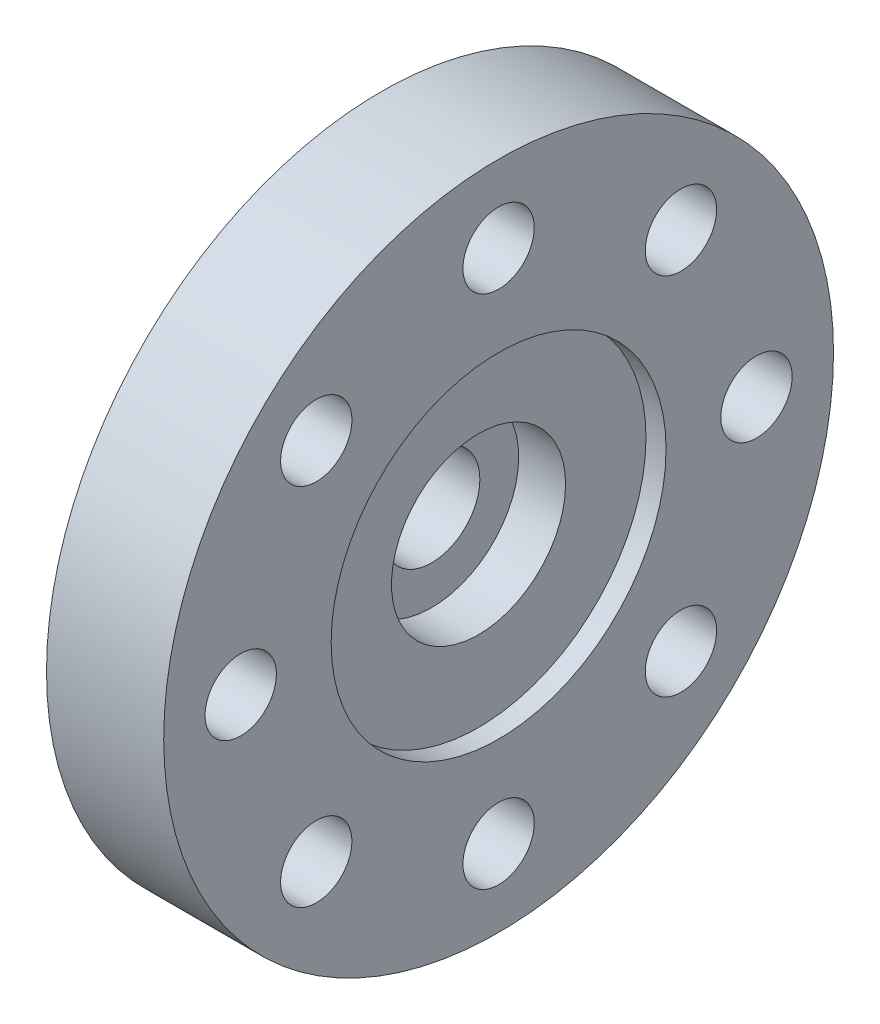
SolidWorks part; units mm, degrees
ref_plane "Front" through (0, 0, 0) normal (0, 0, 1) x (1, 0, 0)
ref_plane "Top" through (0, 0, 0) normal (0, 1, 0) x (1, 0, 0)
ref_plane "Right" through (0, 0, 0) normal (1, 0, 0) x (0, 0, -1)
sketch "Sketch1" plane through (0, 0, 0) normal (1, 0, 0) x (0, 0, -1)
  line L0 (0, 12.7) -> (0, 9.779) construction
  line L1 (0, 12.7) -> (0, 9.779) construction
  circle A0 centre (0, 0) radius 12.7
  circle A1 centre (0, 9.779) radius 1.3525
  circle A2 centre (6.9148, 6.9148) radius 1.3526
  circle A3 centre (9.779, 0) radius 1.3526
  circle A4 centre (6.9148, -6.9148) radius 1.3526
  circle A5 centre (0, -9.779) radius 1.3526
  circle A6 centre (-6.9148, -6.9148) radius 1.3526
  circle A7 centre (-9.779, 0) radius 1.3526
  circle A8 centre (-6.9148, 6.9148) radius 1.3526
  point P22 (0, 0)
  dimension "D1" = 25.4
  dimension "D3" = 2.7051
  dimension "D2" = 2.921
  dimension "D4" = 8
extrude "Boss-Extrude1" add sketch "Sketch1" along normal blind 4.445
sketch "Sketch2" plane through (4.445, 0, 0) normal (1, 0, 0) x (0, 0, -1)
  circle A0 centre (0, 0) radius 6.35
  dimension "D1" = 12.7
extrude "Cut-Extrude1" cut sketch "Sketch2" against normal blind 0.762
sketch "Sketch3" plane through (3.683, 0, 0) normal (1, 0, 0) x (0, 0, -1)
  circle A0 centre (0, 0) radius 3.302
  dimension "D1" = 6.604
extrude "Cut-Extrude2" cut sketch "Sketch3" against normal blind 1.778
sketch "Sketch4" plane through (1.905, 0, 0) normal (1, 0, 0) x (0, 0, -1)
  circle A0 centre (0, 0) radius 1.8288
  dimension "D1" = 3.6576
extrude "Cut-Extrude3" cut sketch "Sketch4" against normal through all
